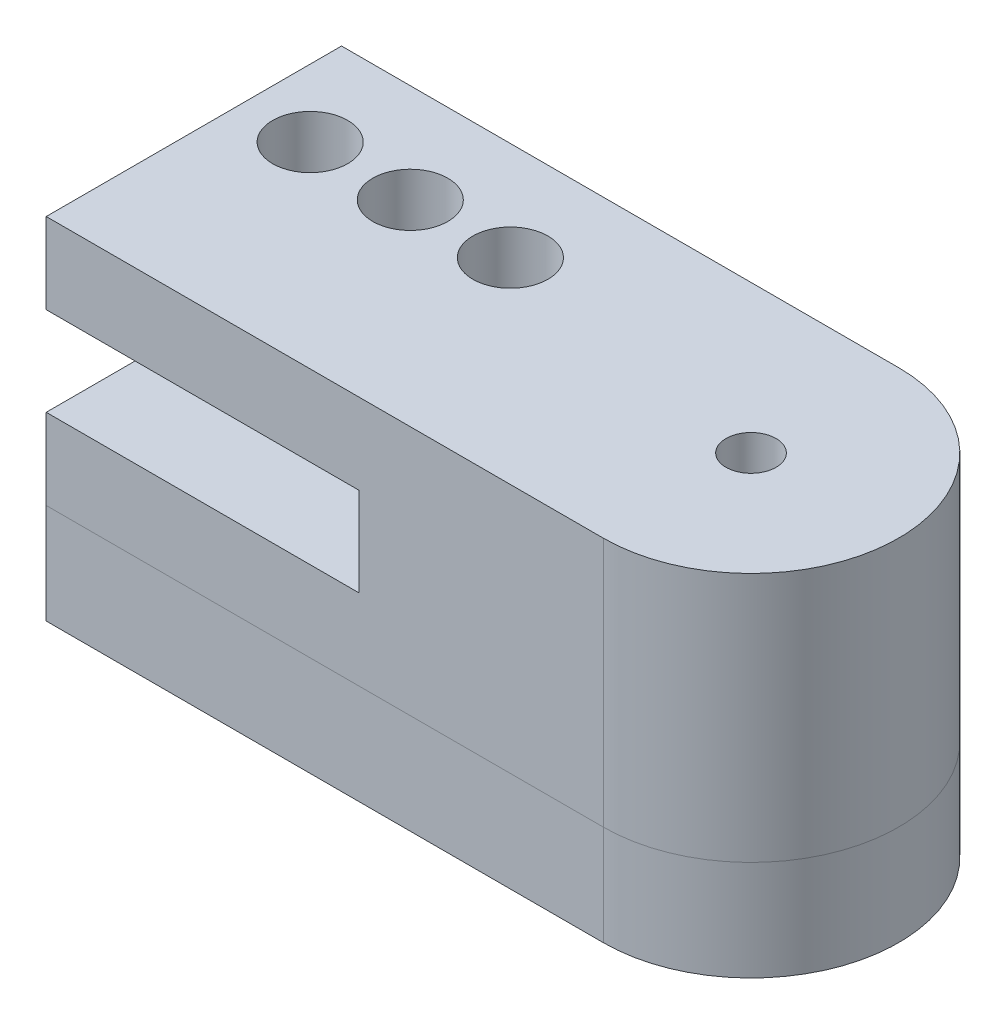
SolidWorks part; units mm, degrees
ref_plane "Front Plane" through (0, 0, 0) normal (0, 0, 1) x (1, 0, 0)
ref_plane "Top Plane" through (0, 0, 0) normal (0, 1, 0) x (1, 0, 0)
ref_plane "Right Plane" through (0, 0, 0) normal (1, 0, 0) x (0, 0, -1)
sketch "Sketch1" plane through (0, 0, 0) normal (0, 1, 0) x (1, 0, 0)
  line L7 (19.8378, 13.8) -> (19.8378, 1.9995)
  line L8 (19.8378, 7.8997) -> (48.0003, 7.8997) construction
  line L11 (19.8378, 13.8) -> (42.1, 13.8)
  line L12 (42.1, 13.8) -> (42.1, 1.9995) construction
  line L13 (19.8378, 1.9995) -> (42.1, 1.9995)
  arc A2 (42.1, 13.8) -> (42.1, 1.9995) centre (42.1, 7.8997) cw
  point P0 (0, 0)
extrude "Boss-Extrude2" add sketch "Sketch1" along normal blind 10
ref_plane "Plane1" through (0, -4, 0) normal (0, -1, 0) x (-1, 0, 0)
sketch "Sketch2" plane through (0, 0, 0) normal (0, 1, 0) x (1, 0, 0)
  line L0 (42.1, 13.8) -> (42.1, 2) construction
  line L5 (26.1498, 7.9) -> (45.7842, 7.9) construction
  line L6 (42.1, 18.1892) -> (42.1, -2.3892) construction
  line L7 (27.9848, 9.8932) -> (39.8678, 10.8763) construction
  line L8 (27.9848, 5.9068) -> (39.8683, 4.9233) construction
  circle A9 centre (42.1, 7.9) radius 3.6842 construction
  arc A16 (27.9848, 9.8932) -> (27.9848, 5.9068) centre (28.1497, 7.9) ccw construction
  arc A17 (39.8678, 10.8763) -> (39.8683, 4.9233) centre (42.1, 7.9) ccw construction
  point P0 (53.3853, 10.5001)
  point P3 (46.1609, 22.3448)
  point P5 (49.6378, 19.3514)
  point P29 (51.9992, 11.3401)
  point P37 (42.1, 7.9)
ref_plane "Plane2" through (0, 0, 0) normal (0, -1, 0) x (-1, 0, 0)
sketch "Sketch4" plane through (0, 0, 0) normal (0, -1, 0) x (-1, 0, 0)
  line L0 (-19.8378, 2) -> (-19.8378, 13.8)
  line L1 (-19.8378, 2) -> (-42.1, 2)
  line L3 (-19.8378, 13.8) -> (-42.1, 13.8)
  line L4 (-42.1, 2) -> (-42.1, 13.8) construction
  arc A0 (-42.1, 2) -> (-42.1, 13.8) centre (-42.1, 7.9) cw
extrude "Boss-Extrude3" add sketch "Sketch4" along normal blind 4
ref_plane "Plane3" through (0, -4, 0) normal (0, -1, 0) x (-1, 0, 0)
sketch "Sketch6" plane through (0, -4, 0) normal (0, -1, 0) x (1, 0, 0)
  line L0 (28.7799, -2.8191) -> (40.5802, -4.5046)
  line L1 (19.8378, -13.8) -> (42.1, -13.8) construction
  line L2 (27.8928, -6.7195) -> (39.2611, -10.3039)
  line L4 (42.1, -7.9) -> (28.3364, -4.7693) construction
  arc A0 (39.2611, -10.3039) -> (40.5802, -4.5046) centre (42.1, -7.9) ccw
  arc A1 (28.7799, -2.8191) -> (27.8928, -6.7195) centre (28.3364, -4.7693) ccw
  dimension "D1" = 4
  dimension "D3" = 7.44
  dimension "D4" = 11.92
  dimension "D2" = 14.1152
  dimension "D5" = 11.92
  dimension "D6" = 17.5
  dimension "D7" = 9.371
extrude "Cut-Extrude1" cut sketch "Sketch6" against normal blind 4
sketch "Sketch7" plane through (0, 0, 0) normal (0, -1, 0) x (1, 0, 0)
  circle A0 centre (42.1, -7.9) radius 1
extrude "Cut-Extrude2" cut sketch "Sketch7" against normal through all
ref_plane "Plane4" through (19.8378, 0, 0) normal (-1, 0, 0) x (0, 0, 1)
sketch "Sketch9" plane through (0, 0, -1.9995) normal (0, 0, 1) x (1, 0, 0)
  line L0 (19.8378, 10) -> (19.8378, 5) construction
  line L1 (19.8378, 10) -> (19.8378, 0) construction
  line L2 (19.8378, 5) -> (32.3378, 5) construction
  line L4 (19.8378, 3.225) -> (32.3378, 3.225)
  line L5 (19.8378, 3.225) -> (19.8378, 6.775)
  line L6 (19.8378, 6.775) -> (32.3378, 6.775)
  line L7 (32.3378, 3.225) -> (32.3378, 6.775)
  line L8 (19.8378, 3.225) -> (32.3378, 6.775) construction
  line L9 (19.8378, 6.775) -> (32.3378, 3.225) construction
  point P6 (26.0878, 5)
extrude "Cut-Extrude7" cut sketch "Sketch9" against normal through all
sketch "Sketch11" plane through (0, 10, 0) normal (0, 1, 0) x (1, 0, 0)
  line L0 (42.1, 7.9) -> (36.3, 7.9) construction
  line L1 (36.3, 13.8) -> (36.3, 9.85) construction
  line L2 (42.1, 13.8) -> (19.8378, 13.8) construction
  line L3 (32.3378, 9.85) -> (30.5349, 9.85) construction
  line L4 (19.8378, 9.85) -> (32.3378, 9.85) construction
  line L5 (19.8378, 13.8) -> (19.8378, 1.9995) construction
  line L6 (19.8378, 9.85) -> (24.0078, 9.85) construction
  circle A1 centre (36.3, 9.85) radius 1.5 construction
  circle A2 centre (30.5349, 9.85) radius 1.5
  circle A3 centre (26.5349, 9.85) radius 1.5
  circle A4 centre (22.5349, 9.85) radius 1.5
  dimension "D1" = 3
extrude "Cut-Extrude8" cut sketch "Sketch11" against normal through all
